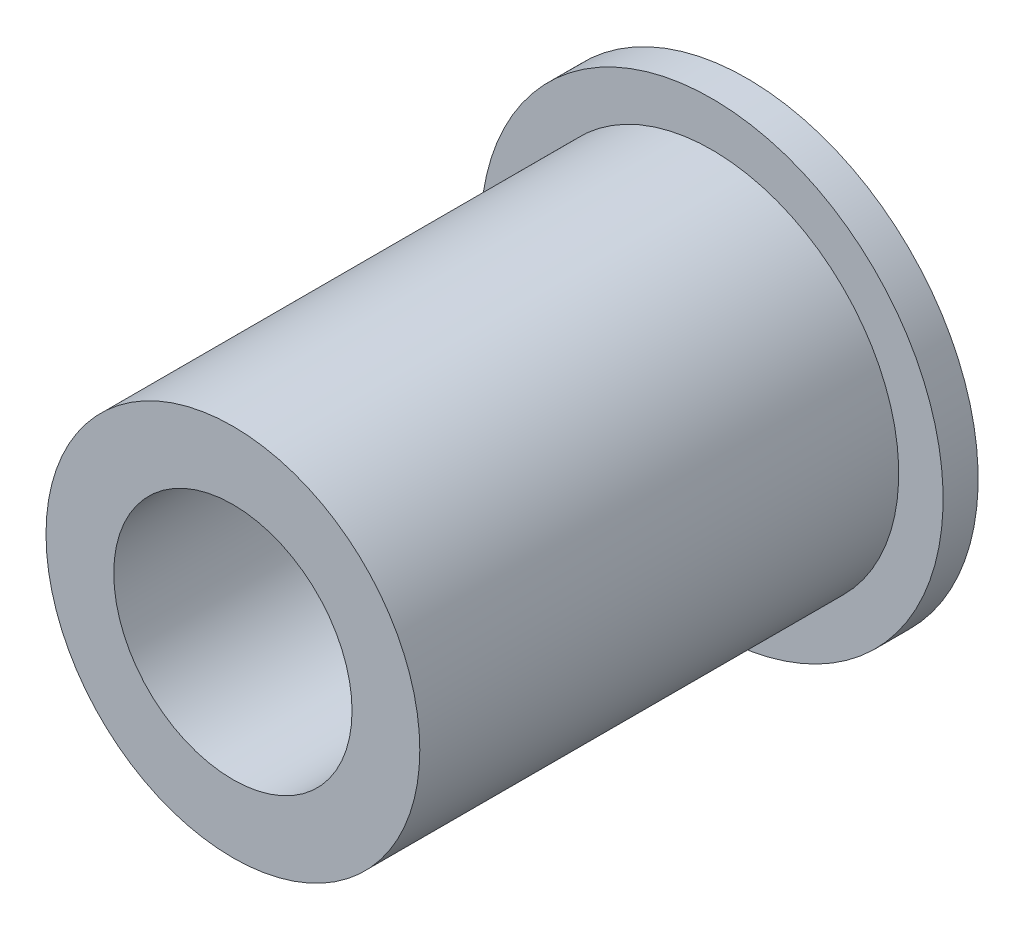
SolidWorks part; units mm, degrees
ref_plane "Front Plane" through (0, 0, 0) normal (0, 0, 1) x (1, 0, 0)
ref_plane "Top Plane" through (0, 0, 0) normal (0, 1, 0) x (1, 0, 0)
ref_plane "Right Plane" through (0, 0, 0) normal (1, 0, 0) x (0, 0, -1)
sketch "Sketch1" plane through (0, 0, 0) normal (0, 0, 1) x (1, 0, 0)
  circle A0 centre (0, 0) radius 8
  dimension "D1" = 16
extrude "Boss-Extrude1" add sketch "Sketch1" along normal blind 22
sketch "Sketch2" plane through (0, 0, 22) normal (0, 0, 1) x (1, 0, 0)
  circle A0 centre (0, 0) radius 5.1
  circle A1 centre (0, 0) radius 8 construction
  dimension "D1" = 2.9
extrude "Cut-Extrude1" cut sketch "Sketch2" against normal blind 13
sketch "Sketch4" plane through (0, 0, 0) normal (0, 0, -1) x (-1, 0, 0)
  circle A0 centre (0, 0) radius 9.9
  dimension "D1" = 19.8
extrude "Boss-Extrude2" add sketch "Sketch4" against normal blind 1.5
sketch "Sketch3" plane through (0, 0, 0) normal (0, 0, -1) x (-1, 0, 0)
  line L0 (-0.8588, 1.35) -> (0.8588, 1.35)
  arc A0 (-0.8588, 1.35) -> (0.8588, 1.35) centre (0, 0) ccw
  dimension "D1" = 3.2
  dimension "D2" = 1.35
extrude "Cut-Extrude2" cut sketch "Sketch3" against normal through all
